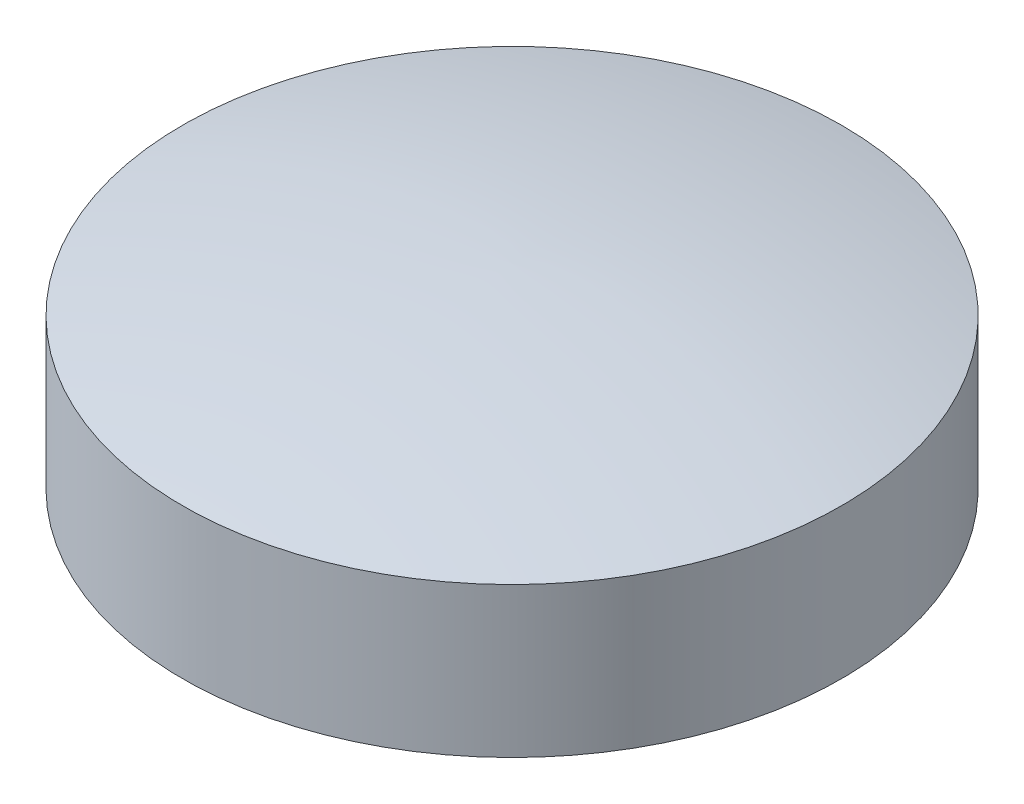
SolidWorks part; units mm, degrees
ref_plane "Front Plane" through (0, 0, 0) normal (0, 0, 1) x (1, 0, 0)
ref_plane "Top Plane" through (0, 0, 0) normal (0, 1, 0) x (1, 0, 0)
ref_plane "Right Plane" through (0, 0, 0) normal (1, 0, 0) x (0, 0, -1)
sketch "Sketch2" plane through (0, 0, 0) normal (0, 0, 1) x (1, 0, 0)
  line L0 (0, 0) -> (0, 26) construction
  line L1 (0, 0) -> (22, 0)
  line L2 (22, 0) -> (22, 10)
  line L3 (0, 0) -> (0, 13)
  arc A0 (0, 13) -> (22, 10) centre (-1.5019, -80.1809) cw
  dimension "D1" = 3
  dimension "D2" = 10
  dimension "D3" = 22
revolve "Revolve1" add sketch "Sketch2" angle 360 about L0
